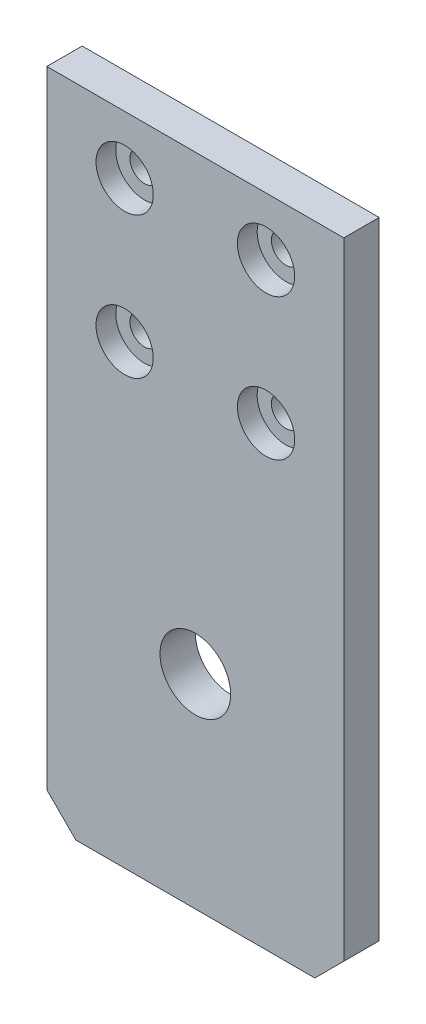
SolidWorks part; units mm, degrees
ref_plane "Alzado" through (0, 0, 0) normal (0, 0, 1) x (1, 0, 0)
ref_plane "Planta" through (0, 0, 0) normal (0, 1, 0) x (1, 0, 0)
ref_plane "Vista lateral" through (0, 0, 0) normal (1, 0, 0) x (0, 0, -1)
sketch "Croquis1" plane through (0, 0, 0) normal (0, 0, 1) x (1, 0, 0)
  line L0 (11, 56.8) -> (31, 76.8) construction
  line L1 (0, 85) -> (42, 85)
  line L2 (0, 85) -> (0, 0)
  line L3 (0, 0) -> (42, 0)
  line L4 (42, 85) -> (42, 0)
  line L5 (21, 66.8) -> (21, 85) construction
  circle A0 centre (11, 76.8) radius 2.05
  circle A1 centre (31, 76.8) radius 2.05
  circle A4 centre (31, 56.8) radius 2.05
  circle A5 centre (11, 56.8) radius 2.05
  dimension "D3" = 4.1
  dimension "D1" = 42
  dimension "D2" = 85
  dimension "D4" = 20
  dimension "D6" = 8.2
  dimension "D7" = 20
extrude "Saliente-Extruir1" add sketch "Croquis1" along normal blind 5
sketch "Croquis4" plane through (0, 0, 5) normal (0, 0, 1) x (1, 0, 0)
  circle A0 centre (11, 76.8) radius 4.05
  circle A1 centre (11, 56.8) radius 4.05
  circle A2 centre (31, 56.8) radius 4.05
  circle A3 centre (31, 76.8) radius 4.05
  dimension "D1" = 8.1
extrude "Cortar-Extruir1" cut sketch "Croquis4" against normal blind 2.8
sketch "Croquis5" plane through (0, 0, 5) normal (0, 0, 1) x (1, 0, 0)
  line L0 (5.5, 36.58) -> (36.5, 5.58) construction
  line L1 (0, 85) -> (42, 85) construction
  line L2 (36.5, 36.58) -> (5.5, 5.58) construction
  line L3 (21, 21.08) -> (21, 0) construction
  line L4 (0, 0) -> (42, 0) construction
  circle A0 centre (21, 21.08) radius 11.5 construction
  circle A1 centre (5.5, 36.58) radius 1.575
  circle A2 centre (36.5, 36.58) radius 1.575
  circle A3 centre (36.5, 5.58) radius 1.575
  circle A4 centre (5.5, 5.58) radius 1.575
  dimension "D1" = 23
  dimension "D4" = 3.15
  dimension "D2" = 31
  dimension "D3" = 31
  dimension "D5" = 63.92
extrude "Cortar-Extruir2" [suppressed] cut sketch "Croquis5" against normal through all
sketch "Croquis6" [suppressed] plane through (0, 0, 5) normal (0, 0, 1) x (1, 0, 0)
  circle A0 centre (5.5, 36.58) radius 3
  circle A1 centre (36.5, 36.58) radius 3
  circle A2 centre (36.5, 5.58) radius 3
  circle A4 centre (5.5, 5.58) radius 3
  dimension "D1" = 6
extrude "Cortar-Extruir3" [suppressed] cut sketch "Croquis6" against normal blind 2.5
sketch "Croquis7" plane through (0, 0, 5) normal (0, 0, 1) x (1, 0, 0)
  line L0 (5.5, 36.58) -> (36.5, 5.58) construction
  circle A0 centre (21, 21.08) radius 5
  dimension "D1" = 10
extrude "Cortar-Extruir4" cut sketch "Croquis7" against normal through all
sketch "Croquis8" plane through (0, 0, 5) normal (0, 0, 1) x (1, 0, 0)
  line L1 (0, 0) -> (42, 0)
  line L2 (0, 0) -> (0, -7.7)
  line L3 (0, -7.7) -> (42, -7.7)
  line L4 (42, 0) -> (42, -7.7)
  dimension "D1" = 7.7
extrude "Saliente-Extruir2" add sketch "Croquis8" against normal through all
chamfer "Chaflán1" distance 4.1 angle 45 2 edges at (42, -7.7, 2.5) (0, -7.7, 2.5)
